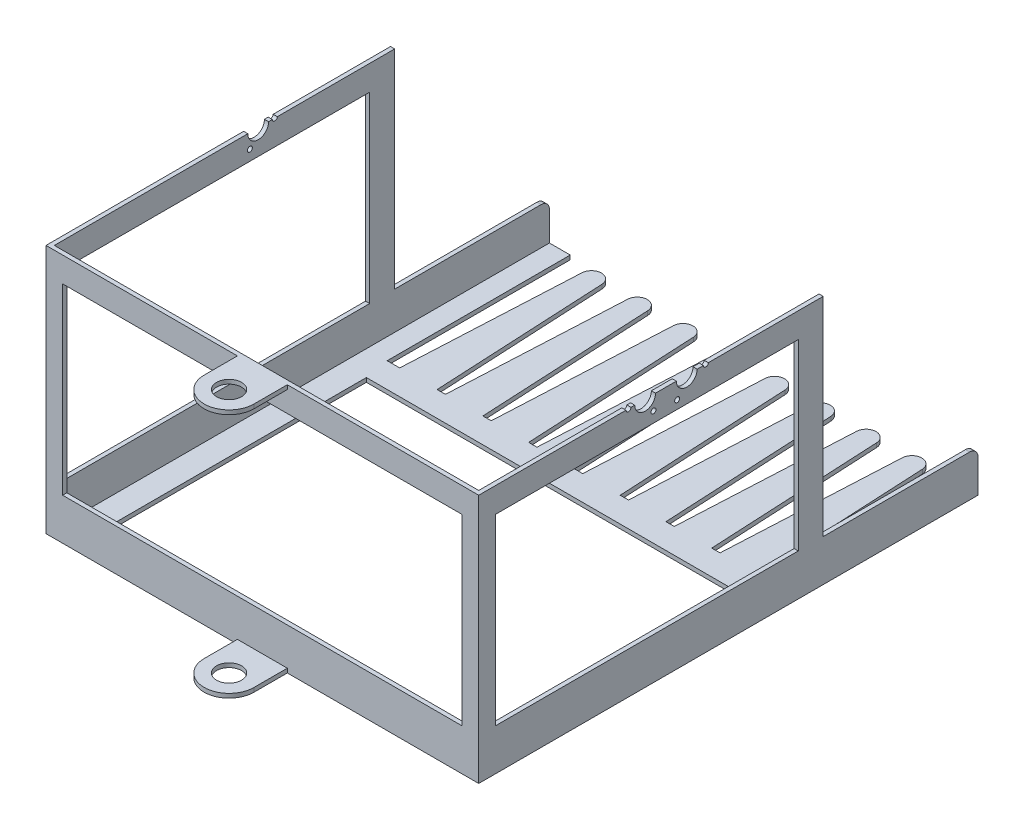
SolidWorks part; units mm, degrees
material "普通碳钢"
ref_plane "前视基准面" through (0, 0, 0) normal (0, 0, 1) x (1, 0, 0)
ref_plane "上视基准面" through (0, 0, 0) normal (0, 1, 0) x (1, 0, 0)
ref_plane "右视基准面" through (0, 0, 0) normal (1, 0, 0) x (0, 0, -1)
sketch "草图1" plane through (0, 0, 0) normal (0, 1, 0) x (1, 0, 0)
  line L0 (-645.6652, 0) -> (638.4717, 0) construction
  line L1 (0, 351.4228) -> (0, -456.7986) construction
  line L2 (-610.83, 80) -> (673.3068, 80) construction
  line L3 (-215, 80) -> (-230, 80)
  line L4 (-260, 300) -> (-260, -300)
  line L5 (-260, -300) -> (260, -300)
  line L6 (260, 300) -> (260, -300)
  line L7 (-230, 80) -> (-230, 300)
  line L8 (-105, 80) -> (-94.4848, 288.6041)
  line L9 (-70.5152, 288.6041) -> (-60, 80)
  line L10 (-260, 300) -> (197.5, 300) construction
  line L11 (-50, 80) -> (-39.4848, 288.6041)
  line L12 (-15.5152, 288.6041) -> (-5, 80)
  line L13 (-192.5, 288) -> (-192.5, 252.85) construction
  line L14 (-215, 80) -> (-204.4848, 288.6041)
  line L15 (5, 80) -> (15.5152, 288.6041)
  line L16 (-180.5152, 288.6041) -> (-170, 80)
  line L17 (-170, 80) -> (-160, 80)
  line L18 (-160, 80) -> (-149.4848, 288.6041)
  line L19 (39.4848, 288.6041) -> (50, 80)
  line L20 (-125.5152, 288.6041) -> (-115, 80)
  line L21 (60, 80) -> (70.5152, 288.6041)
  line L22 (-260, 300) -> (-230, 300)
  line L23 (94.4848, 288.6041) -> (105, 80)
  line L24 (115, 80) -> (125.5152, 288.6041)
  line L25 (149.4848, 288.6041) -> (160, 80)
  line L26 (170, 80) -> (180.5152, 288.6041)
  line L27 (230, 300) -> (260, 300)
  line L28 (204.4848, 288.6041) -> (215, 80)
  line L29 (-192.5, 288) -> (192.6545, 288) construction
  line L30 (215, 80) -> (230, 80)
  line L32 (230, 300) -> (230, 80)
  line L33 (230, 300) -> (260, 300) construction
  line L34 (-115, 80) -> (-105, 80)
  line L35 (-60, 80) -> (-50, 80)
  line L36 (-5, 80) -> (5, 80)
  line L37 (50, 80) -> (60, 80)
  line L38 (105, 80) -> (115, 80)
  line L39 (160, 80) -> (170, 80)
  arc A0 (-70.5152, 288.6041) -> (-94.4848, 288.6041) centre (-82.5, 288) ccw
  arc A1 (-15.5152, 288.6041) -> (-39.4848, 288.6041) centre (-27.5, 288) ccw
  arc A2 (39.4848, 288.6041) -> (15.5152, 288.6041) centre (27.5, 288) ccw
  arc A3 (94.4848, 288.6041) -> (70.5152, 288.6041) centre (82.5, 288) ccw
  arc A4 (149.4848, 288.6041) -> (125.5152, 288.6041) centre (137.5, 288) ccw
  arc A5 (-125.5152, 288.6041) -> (-149.4848, 288.6041) centre (-137.5, 288) ccw
  arc A6 (-180.5152, 288.6041) -> (-204.4848, 288.6041) centre (-192.5, 288) ccw
  arc A7 (204.4848, 288.6041) -> (180.5152, 288.6041) centre (192.5, 288) ccw
  dimension "D5" = 10
  dimension "D6" = 30
  dimension "D7" = 12
  dimension "D4" = 45
  dimension "D1" = 520
  dimension "D2" = 600
  dimension "D3" = 80
  dimension "D8" = 7
  dimension "D9" = 10
extrude "凸台-拉伸1" add sketch "草图1" along normal blind 300
sketch "草图2" plane through (0, 0, 300) normal (0, 0, 1) x (1, 0, 0)
  line L0 (0, 274.4714) -> (0, -97.8508) construction
  line L1 (-260, 300) -> (-260, 0) construction
  line L2 (-240, 50) -> (240, 50)
  line L3 (-240, 50) -> (-240, 270)
  line L4 (-240, 270) -> (240, 270)
  line L5 (240, 50) -> (240, 270)
  line L6 (-240, 50) -> (240, 270) construction
  line L7 (-240, 270) -> (240, 50) construction
  line L8 (-170, 300) -> (-180.5152, 300) construction
  line L9 (-260, 0) -> (260, 0) construction
  point P3 (0, 160)
  point P11 (-175.2576, 300)
  dimension "D1" = 20
  dimension "D2" = 50
  dimension "D3" = 30
extrude "切除-拉伸1" cut sketch "草图2" against normal through all
sketch "草图3" plane through (-260, 0, 0) normal (-1, 0, 0) x (0, 0, 1)
  line L0 (0, 290.5862) -> (0, -126.5752) construction
  line L1 (300, 50) -> (300, 270) construction
  line L2 (-84, 270) -> (280, 270)
  line L3 (-84, 270) -> (-84, 50)
  line L4 (-84, 50) -> (280, 50)
  line L5 (280, 270) -> (280, 50)
  line L6 (-300, 0) -> (300, 0) construction
  line L7 (-300, 300) -> (300, 300) construction
  point P7 (300, 160)
  dimension "D1" = 20
  dimension "D2" = 364
  dimension "D3" = 30
  dimension "D4" = 50
extrude "切除-拉伸2" cut sketch "草图3" against normal up to surface (520 mm away) up to face at (260, 150, 0)
sketch "草图5" plane through (-260, 0, 0) normal (-1, 0, 0) x (0, 0, 1)
  line L0 (-300, 50) -> (-114, 50)
  line L1 (-114, 300) -> (-114, 50)
  line L2 (-300, 300) -> (300, 300) construction
  line L3 (-114, 300) -> (-300, 300)
  line L4 (-300, 50) -> (-300, 300)
  line L5 (-300, 300) -> (300, 300) construction
  line L6 (-300, 300) -> (-300, 0) construction
  line L9 (-84, 270) -> (-84, 50) construction
  line L10 (-84, 50) -> (280, 50) construction
  dimension "D2" = 30
extrude "切除-拉伸4" cut sketch "草图5" against normal up to surface (520 mm away) up to face at (260, 160, 98)
sketch "草图6" plane through (0, 300, 0) normal (0, 1, 0) x (1, 0, 0)
  line L0 (-595.5245, 0) -> (530.7936, 0) construction
  line L1 (0, -363.1405) -> (0, 335.9535) construction
  line L2 (-260, -300) -> (260, -300) construction
  line L3 (-255, 505) -> (255, 505)
  line L4 (-255, 505) -> (-255, -295)
  line L5 (-255, -295) -> (255, -295)
  line L6 (255, 505) -> (255, -295)
  line L7 (-255, 505) -> (255, -295) construction
  line L8 (-255, -295) -> (255, 505) construction
  line L9 (-260, 114) -> (-260, -300) construction
  point P5 (0, 105)
  dimension "D1" = 5
  dimension "D2" = 800
  dimension "D3" = 5
extrude "切除-拉伸5" cut sketch "草图6" against normal offset from surface (295 mm away) 5 up to face at (0, 0, -168.7208)
sketch "草图4" plane through (-260, 0, 0) normal (-1, 0, 0) x (0, 0, 1)
  line L0 (-114, 300) -> (300, 300) construction
  line L1 (300, 300) -> (300, 0) construction
  circle A0 centre (50, 300) radius 12.5
  dimension "D2" = 25
  dimension "D1" = 250
extrude "切除-拉伸3" cut sketch "草图4" against normal up to next
sketch "草图12" plane through (260, 0, 0) normal (1, 0, 0) x (0, 0, -1)
  line L0 (-300, 300) -> (114, 300) construction
  circle A0 centre (-100, 300) radius 12.5
  circle A1 centre (-50, 300) radius 12.5
  dimension "D1" = 50
  dimension "D2" = 25
  dimension "D3" = 25
extrude "切除-拉伸8" cut sketch "草图12" against normal blind 10
sketch "草图7" plane through (0, 300, 0) normal (0, 1, 0) x (1, 0, 0)
  line L0 (0, -514.0254) -> (0, 475.8726) construction
  line L1 (-260, -300) -> (260, -300) construction
  line L2 (-30, -340) -> (-30, -300)
  line L3 (-30, -300) -> (30, -300)
  line L4 (30, -300) -> (30, -340)
  arc A0 (-30, -340) -> (30, -340) centre (0, -340) ccw
  circle A1 centre (0, -340) radius 15
  dimension "D1" = 60
  dimension "D2" = 30
  dimension "D3" = 40
extrude "凸台-拉伸2" add sketch "草图7" against normal up to surface (300 mm away) up to face at (0, 0, -168.7208)
sketch "草图8" plane through (-30, 0, 0) normal (-1, 0, 0) x (0, 0, 1)
  line L0 (300, 270) -> (300, 300) construction
  line L1 (300, 295) -> (477.6214, 295)
  line L2 (300, 295) -> (300, 5)
  line L3 (300, 5) -> (477.6214, 5)
  line L4 (477.6214, 295) -> (477.6214, 5)
  line L5 (300, 300) -> (340, 300) construction
  line L6 (300, 0) -> (340, 0) construction
  point P6 (320, 300)
  dimension "D1" = 5
  dimension "D2" = 5
extrude "切除-拉伸6" cut sketch "草图8" against normal up to next
sketch "草图10" plane through (0, 50, 0) normal (0, 1, 0) x (1, 0, 0)
  line L0 (-337.5799, -284) -> (357.0133, -284) construction
  line L1 (-337.5799, 80) -> (372.1131, 80) construction
  line L2 (-255, -295) -> (-255, 300) construction
  line L3 (-225, 50) -> (225, 50)
  line L4 (-225, 50) -> (-225, -265)
  line L5 (-225, -265) -> (225, -265)
  line L6 (225, 50) -> (225, -265)
  line L7 (255, 300) -> (255, -295) construction
  line L8 (-255, -295) -> (255, -295) construction
  dimension "D1" = 30
  dimension "D2" = 30
  dimension "D3" = 30
  dimension "D4" = 30
extrude "切除-拉伸7" cut sketch "草图10" against normal through all
fillet "圆角1" radius 10 2 edges at (-257.5, 50, -300) (257.5, 50, -300)
sketch "草图13" plane through (260, 0, 0) normal (1, 0, 0) x (0, 0, -1)
  line L0 (300, 20) -> (-300, 20) construction
  line L1 (300, 40) -> (300, 0) construction
  line L2 (-300, 300) -> (-300, 0) construction
  line L3 (-98, 50) -> (-98, 0) construction
  line L4 (-280, 50) -> (84, 50) construction
  circle A0 centre (-198, 20) radius 6
  circle A1 centre (2, 20) radius 6
  dimension "D1" = 12
  dimension "D2" = 200
  dimension "D3" = 30
extrude "切除-拉伸9" [suppressed] cut sketch "草图13" against normal through all
sketch "草图14" plane through (0, 300, 0) normal (0, 1, 0) x (1, 0, 0)
  line L0 (-302.5554, -200) -> (260, -200) construction
  line L1 (30, -300) -> (260, -300) construction
  line L2 (260, -75) -> (372.1769, -75) construction
  line L3 (260, -300) -> (260, -112.5) construction
  line L4 (280, -215) -> (260, -215)
  line L5 (280, -185) -> (260, -185)
  line L6 (285, -200) -> (303.8215, -200) construction
  line L7 (260, -87.5) -> (260, -62.5) construction
  line L8 (280, 65) -> (260, 65)
  line L9 (280, 35) -> (260, 35)
  line L10 (0, -340) -> (0, 0) construction
  line L11 (-280, -215) -> (-260, -215)
  line L12 (-280, -185) -> (-260, -185)
  line L13 (-280, 35) -> (-260, 35)
  line L14 (-280, 65) -> (-260, 65)
  line L15 (260, -185) -> (260, -215)
  line L16 (260, 65) -> (260, 35)
  line L17 (-260, -185) -> (-260, -215)
  line L18 (-260, 65) -> (-260, 35)
  circle A0 centre (280, -200) radius 5
  arc A1 (280, -215) -> (280, -185) centre (280, -200) ccw
  circle A2 centre (280, 50) radius 5
  arc A3 (280, 65) -> (280, 35) centre (280, 50) cw
  circle A4 centre (-280, -200) radius 5
  arc A5 (-280, -215) -> (-280, -185) centre (-280, -200) cw
  circle A6 centre (-280, 50) radius 5
  arc A7 (-280, 65) -> (-280, 35) centre (-280, 50) ccw
  dimension "D2" = 20
  dimension "D3" = 15
  dimension "D4" = 10
  dimension "D1" = 100
extrude "凸台-拉伸3" [suppressed] add sketch "草图14" against normal blind 5
sketch "草图15" plane through (260, 0, 0) normal (1, 0, 0) x (0, 0, -1)
  circle A0 centre (-100, 300) radius 20 construction
  circle A1 centre (-120, 300) radius 3
  circle A2 centre (-90, 317.3205) radius 3 construction
  circle A3 centre (-90, 282.6795) radius 3
  point P11 (-100, 300)
  point P12 (-100, 300)
  dimension "D1" = 6
  dimension "D2" = 40
  dimension "D3" = 3
extrude "切除-拉伸10" cut sketch "草图15" against normal up to surface (5 mm away) up to face at (255, 175.1883, -20.9156)
sketch "草图16" plane through (-260, 0, 0) normal (-1, 0, 0) x (0, 0, 1)
  circle A0 centre (50, 300) radius 20 construction
  circle A1 centre (30, 300) radius 3
  circle A2 centre (60, 317.3205) radius 3 construction
  circle A3 centre (60, 282.6795) radius 3
  point P11 (50, 300)
  dimension "D1" = 40
  dimension "D2" = 6
  dimension "D3" = 3
extrude "切除-拉伸11" cut sketch "草图16" against normal up to surface (5 mm away) up to face at (-255, 148.8412, -47.7857)
sketch "草图17" plane through (260, 0, 0) normal (1, 0, 0) x (0, 0, -1)
  circle A0 centre (-50, 300) radius 23 construction
  circle A1 centre (-27, 300) radius 3
  circle A2 centre (-61.5, 280.0814) radius 3
  circle A3 centre (-61.5, 319.9186) radius 3 construction
  point P12 (-50, 300)
  dimension "D1" = 46
  dimension "D2" = 6
  dimension "D3" = 3
extrude "切除-拉伸12" cut sketch "草图17" against normal up to surface (5 mm away) up to face at (255, 282.6795, 87)
